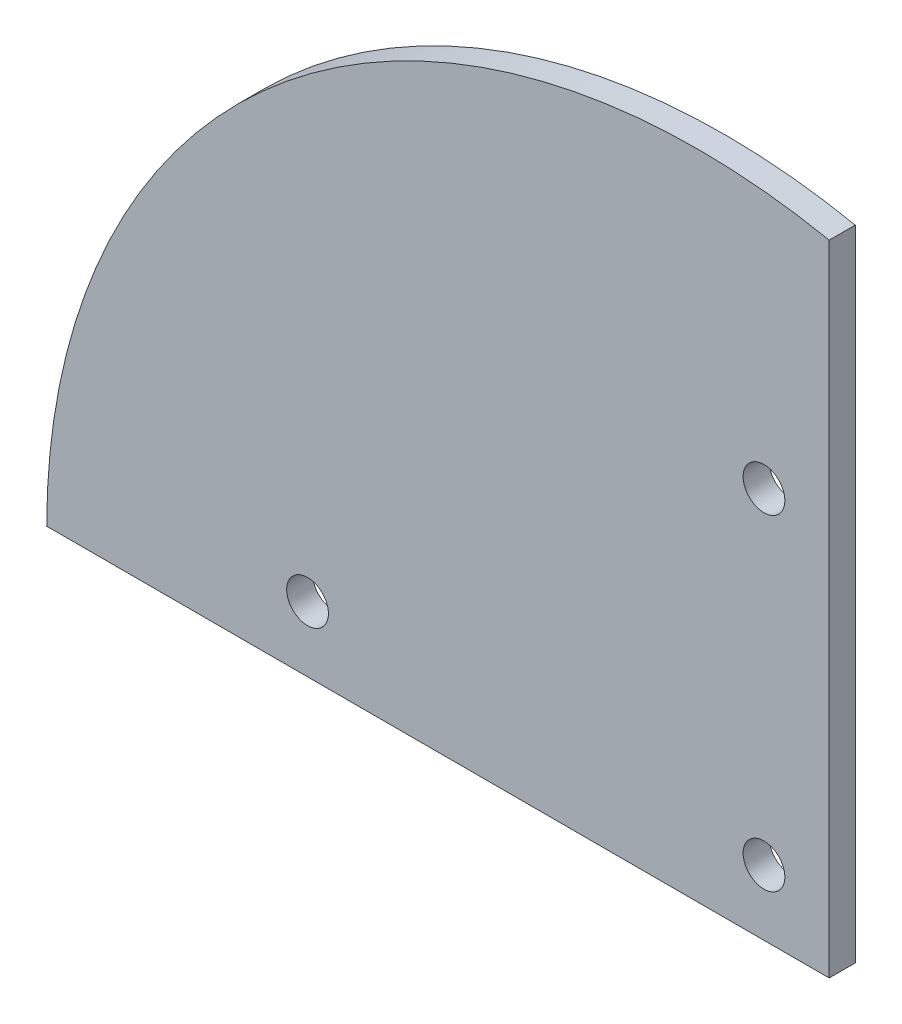
SolidWorks part; units mm, degrees
material "Bearbeitungsplatte, Einfach"
ref_plane "Ebene vorne" through (0, 0, 0) normal (0, 0, 1) x (1, 0, 0)
ref_plane "Ebene oben" through (0, 0, 0) normal (0, 1, 0) x (1, 0, 0)
ref_plane "Ebene rechts" through (0, 0, 0) normal (1, 0, 0) x (0, 0, -1)
sketch "Model" plane through (0, 0, 0) normal (0, 0, 1) x (1, 0, 0)
  line L0 (0, 0) -> (60, 0)
  line L1 (60, 0) -> (60, 49)
  arc A0 (60, 49) -> (0, 0) centre (50.005, 0.0041) ccw
  circle A1 centre (55, 5) radius 1.6
  circle A2 centre (55, 30) radius 1.6
  circle A3 centre (20, 5) radius 1.6
extrude "Aufsatz-Linear austragen1" add sketch "Model" along normal blind 2 contours L1 A0 L0 A3 A2 A1
